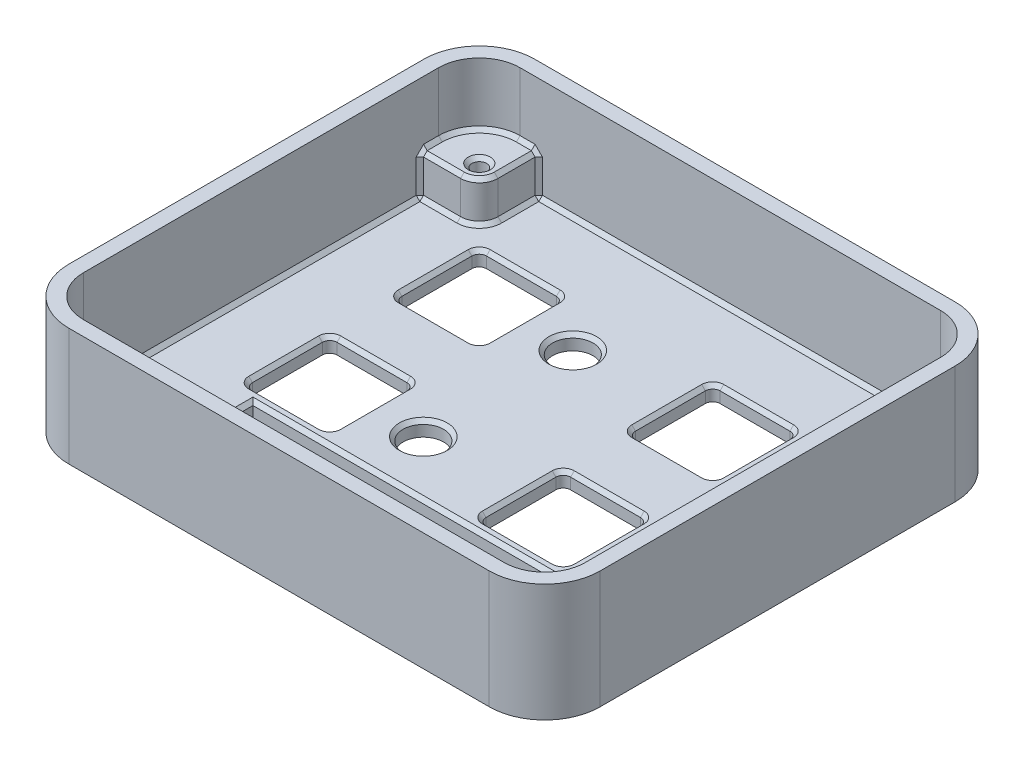
SolidWorks part; units mm, degrees
ref_plane "Front Plane" through (0, 0, 0) normal (0, 0, 1) x (1, 0, 0)
ref_plane "Top Plane" through (0, 0, 0) normal (0, 1, 0) x (1, 0, 0)
ref_plane "Right Plane" through (0, 0, 0) normal (1, 0, 0) x (0, 0, -1)
sketch "Sketch1" plane through (0, 0, 0) normal (0, 1, 0) x (1, 0, 0)
  line L1 (36.115, -31.67) -> (-36.115, -31.67)
  line L2 (36.115, -31.67) -> (36.115, 31.67)
  line L3 (36.115, 31.67) -> (-36.115, 31.67)
  line L4 (-36.115, -31.67) -> (-36.115, 31.67)
  line L5 (36.115, -31.67) -> (-36.115, 31.67) construction
  line L6 (36.115, 31.67) -> (-36.115, -31.67) construction
  point P0 (0, 0)
  dimension "D1" = 63.34
  dimension "D2" = 72.23
extrude "Boss-Extrude1" add sketch "Sketch1" along normal blind 16
fillet "Fillet1" radius 7.54 4 edges at (-36.115, 8, 31.67) (36.115, 8, 31.67) (36.115, 8, -31.67) (-36.115, 8, -31.67)
shell "Shell1" thickness 2
sketch "Sketch2" plane through (0, 0, 0) normal (0, 1, 0) x (1, 0, 0)
  line L0 (-12.685, 13.97) -> (-5.705, 13.97) construction
  line L1 (-23.185, 19.72) -> (-13.685, 19.72)
  line L2 (-24.185, 18.72) -> (-24.185, 9.22)
  line L3 (-23.185, 8.22) -> (-13.685, 8.22)
  line L4 (-12.685, 18.72) -> (-12.685, 9.22)
  line L5 (-36.115, 24.13) -> (-36.115, -24.13) construction
  line L6 (-28.575, -31.67) -> (28.575, -31.67) construction
  line L7 (8.565, 19.72) -> (18.065, 19.72)
  line L8 (7.565, 18.72) -> (7.565, 9.22)
  line L9 (19.065, 18.72) -> (19.065, 9.22)
  line L10 (8.565, 8.22) -> (18.065, 8.22)
  line L11 (8.565, -0.6) -> (18.065, -0.6)
  line L12 (7.565, -1.6) -> (7.565, -11.1)
  line L13 (19.065, -1.6) -> (19.065, -11.1)
  line L14 (8.565, -12.1) -> (18.065, -12.1)
  line L15 (-23.185, -0.6) -> (-13.685, -0.6)
  line L16 (-24.185, -1.6) -> (-24.185, -11.1)
  line L17 (-12.685, -1.6) -> (-12.685, -11.1)
  line L18 (-23.185, -12.1) -> (-13.685, -12.1)
  line L19 (-24.185, 19.72) -> (7.565, 19.72) construction
  line L20 (-24.185, 19.72) -> (-24.185, -0.6) construction
  line L22 (-21.455, -13.762) -> (20.185, -13.762)
  line L23 (-21.455, -13.762) -> (-21.455, -24.562)
  line L24 (-21.455, -24.562) -> (20.185, -24.562)
  line L25 (20.185, -13.762) -> (20.185, -24.562)
  line L26 (28.575, 31.67) -> (-28.575, 31.67) construction
  line L27 (-21.455, -13.762) -> (20.185, -24.562) construction
  line L28 (-21.455, -24.562) -> (20.185, -13.762) construction
  line L29 (-18.435, 19.72) -> (-18.435, 8.22) construction
  line L30 (-36.115, 24.13) -> (-36.115, -24.13) construction
  line L31 (36.115, -24.13) -> (36.115, 24.13) construction
  circle A0 centre (-5.705, 13.97) radius 2.75
  circle A1 centre (26.045, 13.97) radius 2.75
  circle A2 centre (26.045, -6.35) radius 2.75
  circle A3 centre (-5.705, -6.35) radius 2.75
  arc A4 (19.065, -11.1) -> (18.065, -12.1) centre (18.065, -11.1) cw
  arc A5 (18.065, -0.6) -> (19.065, -1.6) centre (18.065, -1.6) cw
  arc A6 (8.565, -0.6) -> (7.565, -1.6) centre (8.565, -1.6) ccw
  arc A7 (7.565, -11.1) -> (8.565, -12.1) centre (8.565, -11.1) ccw
  arc A8 (-12.685, -11.1) -> (-13.685, -12.1) centre (-13.685, -11.1) cw
  arc A9 (-24.185, -11.1) -> (-23.185, -12.1) centre (-23.185, -11.1) ccw
  arc A10 (-23.185, -0.6) -> (-24.185, -1.6) centre (-23.185, -1.6) ccw
  arc A11 (-13.685, -0.6) -> (-12.685, -1.6) centre (-13.685, -1.6) cw
  arc A12 (18.065, 19.72) -> (19.065, 18.72) centre (18.065, 18.72) cw
  arc A13 (19.065, 9.22) -> (18.065, 8.22) centre (18.065, 9.22) cw
  arc A14 (7.565, 9.22) -> (8.565, 8.22) centre (8.565, 9.22) ccw
  arc A15 (8.565, 19.72) -> (7.565, 18.72) centre (8.565, 18.72) ccw
  arc A16 (-24.185, 9.22) -> (-23.185, 8.22) centre (-23.185, 9.22) ccw
  arc A17 (-13.685, 8.22) -> (-12.685, 9.22) centre (-13.685, 9.22) ccw
  arc A18 (-13.685, 19.72) -> (-12.685, 18.72) centre (-13.685, 18.72) cw
  arc A19 (-23.185, 19.72) -> (-24.185, 18.72) centre (-23.185, 18.72) ccw
  point P10 (-0.635, -19.162)
  point P51 (-24.185, -0.6)
  point P62 (7.565, 19.72)
  point P69 (-12.685, 19.72)
  point P72 (-24.185, 19.72)
  dimension "D6" = 5.5
  dimension "D15" = 1
  dimension "D2" = 30.41
  dimension "D3" = 17.7
  dimension "D4" = 11.5
  dimension "D5" = 7.108
  dimension "D9" = 31.75
  dimension "D10" = 20.32
  dimension "D11" = 10.8
  dimension "D12" = 41.64
  dimension "D13" = 17.68
  dimension "D14" = 36.75
  dimension "D7" = 2
  dimension "D8" = 2
extrude "Cut-Extrude1" cut sketch "Sketch2" along normal through all
sketch "Sketch3" plane through (0, 2, 0) normal (0, 1, 0) x (1, 0, 0)
  line L0 (28.575, -24.13) -> (-28.575, -24.13) construction
  line L1 (-28.575, -24.13) -> (-28.575, 24.13) construction
  line L2 (28.575, 31.67) -> (-28.575, 31.67) construction
  line L3 (-28.575, 21.59) -> (-35.115, 21.59)
  line L4 (-26.035, 24.13) -> (-26.035, 30.67)
  line L5 (-28.575, 24.13) -> (28.575, 24.13) construction
  line L6 (28.575, 24.13) -> (28.575, -24.13) construction
  line L7 (-26.035, 30.67) -> (-28.575, 30.67)
  line L8 (-35.115, 21.59) -> (-35.115, 24.13)
  line L9 (-36.115, 24.13) -> (-36.115, -24.13) construction
  line L10 (28.575, 29.67) -> (-28.575, 29.67) construction
  line L11 (-34.115, 24.13) -> (-34.115, -24.13) construction
  line L12 (-28.575, -29.67) -> (28.575, -29.67) construction
  line L13 (34.115, -24.13) -> (34.115, 24.13) construction
  line L15 (-28.575, -30.67) -> (-26.035, -30.67)
  line L16 (-35.115, -24.13) -> (-35.115, -21.59)
  line L17 (-35.115, -21.59) -> (-28.575, -21.59)
  line L18 (-26.035, -30.67) -> (-26.035, -24.13)
  line L19 (28.575, -21.59) -> (35.115, -21.59)
  line L20 (26.035, -24.13) -> (26.035, -30.67)
  line L21 (26.035, -30.67) -> (28.575, -30.67)
  line L22 (35.115, -21.59) -> (35.115, -24.13)
  line L23 (28.575, 30.67) -> (26.035, 30.67)
  line L24 (35.115, 24.13) -> (35.115, 21.59)
  line L25 (35.115, 21.59) -> (28.575, 21.59)
  line L26 (26.035, 30.67) -> (26.035, 24.13)
  line L27 (-28.575, -31.67) -> (28.575, -31.67) construction
  line L28 (36.115, -24.13) -> (36.115, 24.13) construction
  circle A0 centre (-28.575, 24.13) radius 1
  circle A1 centre (-28.575, -24.13) radius 1
  circle A2 centre (28.575, -24.13) radius 1
  circle A3 centre (28.575, 24.13) radius 1
  arc A4 (-28.575, -21.59) -> (-26.035, -24.13) centre (-28.575, -24.13) cw
  arc A5 (28.575, -21.59) -> (26.035, -24.13) centre (28.575, -24.13) ccw
  arc A6 (28.575, 21.59) -> (26.035, 24.13) centre (28.575, 24.13) cw
  arc A7 (-28.575, 21.59) -> (-26.035, 24.13) centre (-28.575, 24.13) ccw
  arc A8 (-28.575, -30.67) -> (-35.115, -24.13) centre (-28.575, -24.13) cw
  arc A9 (28.575, -30.67) -> (35.115, -24.13) centre (28.575, -24.13) ccw
  arc A10 (28.575, 30.67) -> (35.115, 24.13) centre (28.575, 24.13) cw
  arc A11 (-28.575, 30.67) -> (-35.115, 24.13) centre (-28.575, 24.13) ccw
  point P14 (-25.425, -20.98)
  point P55 (35.115, 30.67)
  dimension "D5" = 2
  dimension "D14" = 2
  dimension "D21" = 2
  dimension "D28" = 2
  dimension "D8" = 2.54
  dimension "D4" = 1
  dimension "D12" = 5.54
  dimension "D16" = 2.54
  dimension "D27" = 2.54
  dimension "D33" = 6.54
  dimension "D6" = 1
  dimension "D7" = 2.54
  dimension "D9" = 5.54
  dimension "D10" = 5.54
  dimension "D11" = 5.54
  dimension "D13" = 1
  dimension "D15" = 1
  dimension "D17" = 2.54
  dimension "D18" = 1
  dimension "D19" = 1
  dimension "D20" = 2.54
  dimension "D22" = 2.54
  dimension "D23" = 1
  dimension "D24" = 1
  dimension "D25" = 2.54
  dimension "D26" = 2.54
  dimension "D29" = 48.26
  dimension "D30" = 57.15
  dimension "D31" = 57.15
  dimension "D32" = 48.26
extrude "Boss-Extrude2" add sketch "Sketch3" along normal blind 5.5
chamfer "Chamfer1" distance 0.5 angle 45 92 edges at (31.345, 2, 21.59) (26.7789, 2, 22.3339) (26.035, 2, 26.9) (0, 2, 29.67) (-26.035, 2, 26.9) (-26.7789, 2, 22.3339) (-31.345, 2, 21.59) (-34.115, 2, 0) (-31.345, 2, -21.59) (-26.7789, 2, -22.3339) (-26.035, 2, -26.9) (0, 2, -29.67) (26.035, 2, -26.9) (26.7789, 2, -22.3339) (31.345, 2, -21.59) (34.115, 2, 0) (-5.705, 2, -11.22) (26.045, 2, -11.22) (26.045, 2, 9.1) (-5.705, 2, 9.1) (19.065, 2, 6.35) (18.7721, 2, 0.8929) (13.315, 2, 0.6) (7.8579, 2, 0.8929) (7.565, 2, 6.35) (7.8579, 2, 11.8071) (13.315, 2, 12.1) (18.7721, 2, 11.8071) (-12.685, 2, 6.35) (-12.9779, 2, 0.8929) (-18.435, 2, 0.6) (-23.8921, 2, 0.8929) (-24.185, 2, 6.35) (-23.8921, 2, 11.8071) (-18.435, 2, 12.1) (-12.9779, 2, 11.8071) (13.315, 2, -19.72) (7.8579, 2, -19.4271) (7.565, 2, -13.97) (7.8579, 2, -8.5129) (13.315, 2, -8.22) (18.7721, 2, -8.5129) (19.065, 2, -13.97) (18.7721, 2, -19.4271) (-18.435, 2, -8.22) (-12.9779, 2, -8.5129) (-12.685, 2, -13.97) (-12.9779, 2, -19.4271) (-18.435, 2, -19.72) (-23.8921, 2, -19.4271) (-24.185, 2, -13.97) (-23.8921, 2, -8.5129) (-28.575, 7.5, 25.13) (-34.115, 4.75, 21.59) (-26.035, 4.75, 29.67) (-31.345, 7.5, 21.59) (-26.7789, 7.5, 22.3339) (-26.035, 7.5, 26.9) (-27.305, 7.5, 29.67) (-32.4924, 7.5, 28.0474) (-34.115, 7.5, 22.86) (28.575, 7.5, -23.13) (34.115, 4.75, -21.59) (26.035, 4.75, -29.67) (31.345, 7.5, -21.59) (26.7789, 7.5, -22.3339) (26.035, 7.5, -26.9) (27.305, 7.5, -29.67) (32.4924, 7.5, -28.0474) (34.115, 7.5, -22.86) (-28.575, 7.5, -23.13) (-26.035, 4.75, -29.67) (-34.115, 4.75, -21.59) (-27.305, 7.5, -29.67) (-26.035, 7.5, -26.9) (-26.7789, 7.5, -22.3339) (-31.345, 7.5, -21.59) (-34.115, 7.5, -22.86) (-32.4924, 7.5, -28.0474) (28.575, 7.5, 25.13) (34.115, 4.75, 21.59) (26.035, 4.75, 29.67) (26.7789, 7.5, 22.3339) (31.345, 7.5, 21.59) (34.115, 7.5, 22.86) (32.4924, 7.5, 28.0474) (27.305, 7.5, 29.67) (26.035, 7.5, 26.9) (-0.635, 2, 13.762) (-21.455, 2, 19.162) (-0.635, 2, 24.562) (20.185, 2, 19.162)
